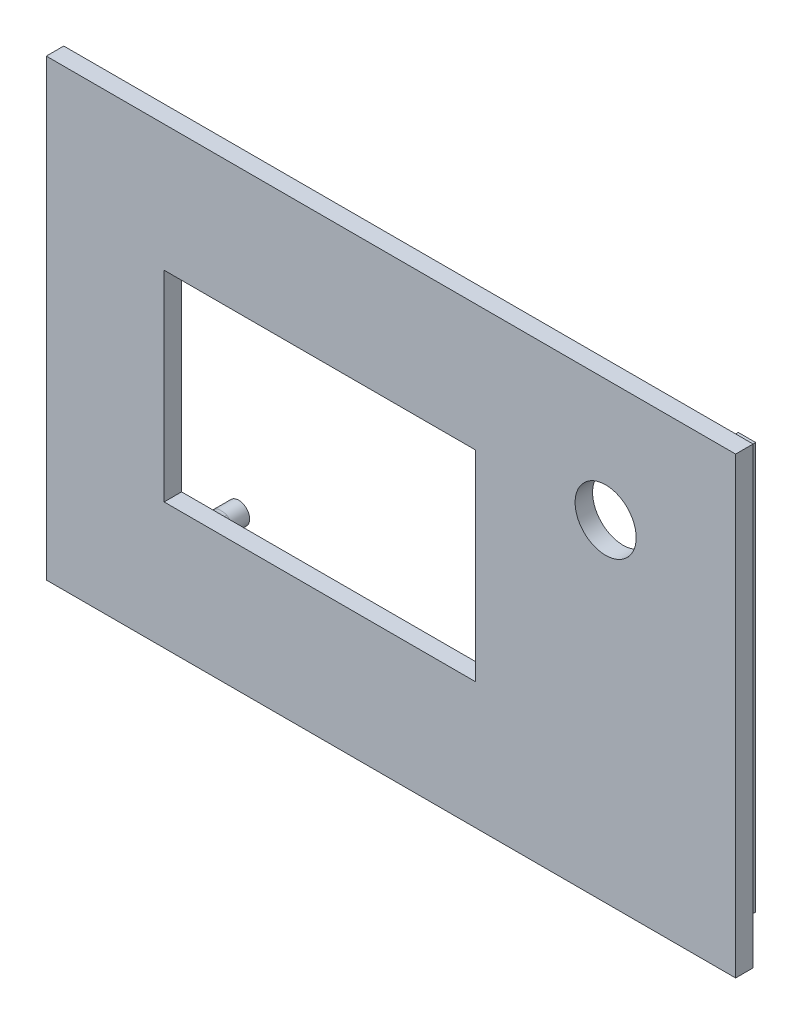
SolidWorks part; units mm, degrees
ref_plane "Ebene vorne" through (0, 0, 0) normal (0, 0, 1) x (1, 0, 0)
ref_plane "Ebene oben" through (0, 0, 0) normal (0, 1, 0) x (1, 0, 0)
ref_plane "Ebene rechts" through (0, 0, 0) normal (1, 0, 0) x (0, 0, -1)
sketch "Skizze10" plane through (0, 0, 0) normal (0, 0, 1) x (1, 0, 0)
  line L1 (-59.4904, -2.4023) -> (19.5096, -2.4023)
  line L2 (-59.4904, -2.4023) -> (-59.4904, -54.4023)
  line L3 (-59.4904, -54.4023) -> (19.5096, -54.4023)
  line L4 (19.5096, -2.4023) -> (19.5096, -54.4023)
  dimension "D1" = 79
  dimension "D2" = 52
extrude "Aufsatz-Linear austragen8" add sketch "Skizze10" along normal blind 2
sketch "Skizze11" plane through (0, 0, 2) normal (0, 0, 1) x (1, 0, 0)
  line L0 (-53.3332, -28.4023) -> (19.5096, -28.4023) construction
  line L1 (-45.987, -16.9023) -> (-10.287, -16.9023)
  line L2 (-45.987, -16.9023) -> (-45.987, -39.9023)
  line L3 (-45.987, -39.9023) -> (-10.287, -39.9023)
  line L4 (-10.287, -16.9023) -> (-10.287, -39.9023)
  line L5 (19.5096, -54.4023) -> (19.5096, -2.4023) construction
  dimension "D1" = 35.7
  dimension "D2" = 23
extrude "Schnitt-Linear austragen3" cut sketch "Skizze11" against normal blind 2
sketch "Skizze13" plane through (0, 0, 2) normal (0, 0, 1) x (1, 0, 0)
  line L0 (4.6113, 9.8264) -> (4.6113, -44.9541) construction
  line L2 (19.5096, -2.4023) -> (-59.4904, -2.4023) construction
  line L3 (19.5096, -54.4023) -> (19.5096, -2.4023) construction
  line L4 (-10.287, -39.9023) -> (-10.287, -16.9023) construction
  circle A0 centre (4.6113, -16.4023) radius 3.5
  dimension "D1" = 7
  dimension "D3" = 14
extrude "Schnitt-Linear austragen4" cut sketch "Skizze13" against normal blind 2 contours A0
sketch "Skizze14" plane through (0, 0, 0) normal (0, 0, -1) x (-1, 0, 0)
  line L0 (43.437, -7.9679) -> (43.437, -51.5306) construction
  line L1 (4.6842, -14.1023) -> (47.1284, -14.1023) construction
  line L3 (12.837, -5.7609) -> (12.837, -48.8799) construction
  line L4 (2.5413, -42.7023) -> (53.5844, -42.7023) construction
  line L5 (28.137, -6.7951) -> (28.137, -49.377) construction
  line L6 (10.287, -39.9023) -> (10.287, -16.9023) construction
  line L7 (45.987, -16.9023) -> (45.987, -39.9023) construction
  line L8 (-10.215, -28.4023) -> (57.4151, -28.4023) construction
  line L9 (10.287, -16.9023) -> (45.987, -16.9023) construction
  line L10 (45.987, -39.9023) -> (10.287, -39.9023) construction
  circle A0 centre (43.437, -14.1023) radius 1.25
  circle A1 centre (43.437, -42.7023) radius 1.25
  circle A2 centre (12.837, -14.1023) radius 1.25
  circle A3 centre (12.837, -42.7023) radius 1.25
  dimension "D1" = 2.5
  dimension "D6" = 2.5
  dimension "D7" = 2.5
  dimension "D8" = 2.5
  dimension "D2" = 30.6
  dimension "D3" = 28.6
extrude "Aufsatz-Linear austragen9" add sketch "Skizze14" along normal blind 4
sketch "Skizze15" plane through (0, 0, 0) normal (0, 0, -1) x (-1, 0, 0)
  line L0 (-16.8096, -5.1023) -> (-16.8096, -51.7023)
  line L1 (-16.8096, -51.7023) -> (56.7904, -51.7023)
  line L4 (59.4904, -54.4023) -> (59.4904, -2.4023)
  line L5 (59.4904, -2.4023) -> (-19.5096, -2.4023)
  line L6 (-19.5096, -2.4023) -> (-19.5096, -54.4023)
  line L7 (-19.5096, -54.4023) -> (59.4904, -54.4023)
  line L10 (-19.5096, -2.4023) -> (-19.5096, -54.4023) construction
  line L11 (-19.5096, -54.4023) -> (59.4904, -54.4023) construction
  line L12 (56.7904, -5.1023) -> (-16.8096, -5.1023) construction
  line L13 (56.7904, -51.7023) -> (56.7904, -5.1023) construction
  line L14 (59.4904, -54.4023) -> (59.4904, -2.4023) construction
  line L15 (59.4904, -2.4023) -> (-19.5096, -2.4023) construction
  line L16 (-14.8096, -5.1023) -> (-14.8096, -49.7023)
  line L17 (-14.8096, -49.7023) -> (56.7904, -49.7023)
  line L18 (-16.8096, -5.1023) -> (-14.8096, -5.1023)
  line L19 (56.7904, -51.7023) -> (56.7904, -49.7023)
  dimension "D1" = 0
  dimension "D2" = 2.7
  dimension "D3" = 2
extrude "Aufsatz-Linear austragen10" add sketch "Skizze15" along normal blind 3
fillet "Verrundung1" radius 2 4 edges at (-11.587, -42.7023, 0) (-42.187, -42.7023, 0) (-42.187, -14.1023, 0) (-11.587, -14.1023, 0)
